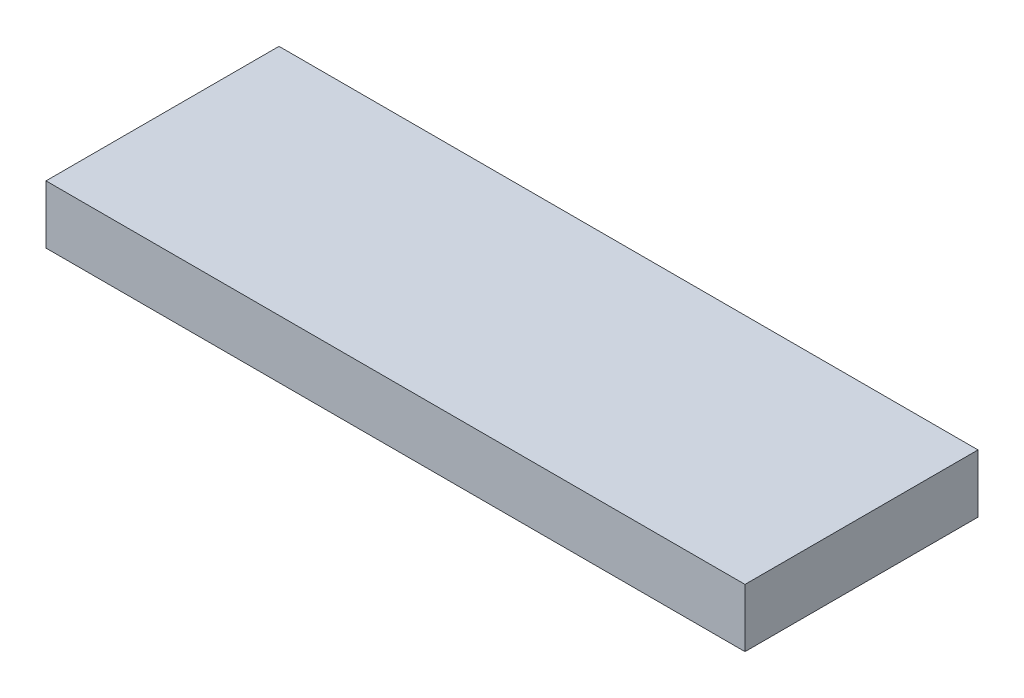
SolidWorks part; units mm, degrees
ref_plane "Front Plane" through (0, 0, 0) normal (0, 0, 1) x (1, 0, 0)
ref_plane "Top Plane" through (0, 0, 0) normal (0, 1, 0) x (1, 0, 0)
ref_plane "Right Plane" through (0, 0, 0) normal (1, 0, 0) x (0, 0, -1)
sketch "Sketch1" plane through (0, 0, 0) normal (0, 1, 0) x (1, 0, 0)
  line L1 (-60, 20) -> (60, 20)
  line L2 (-60, 20) -> (-60, -20)
  line L3 (-60, -20) -> (60, -20)
  line L4 (60, 20) -> (60, -20)
  line L5 (-60, 20) -> (60, -20) construction
  line L6 (-60, -20) -> (60, 20) construction
  point P0 (0, 0)
  dimension "D1" = 40
  dimension "D2" = 120
extrude "Boss-Extrude1" add sketch "Sketch1" along normal blind 10
